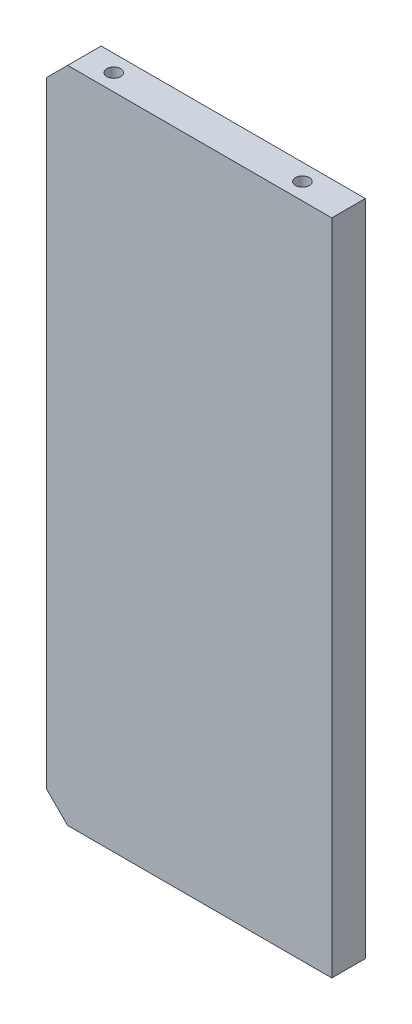
SolidWorks part; units mm, degrees
ref_plane "Front" through (0, 0, 0) normal (0, 0, 1) x (1, 0, 0)
ref_plane "Top" through (0, 0, 0) normal (0, 1, 0) x (1, 0, 0)
ref_plane "Right" through (0, 0, 0) normal (1, 0, 0) x (0, 0, -1)
sketch "Sketch1" plane through (0, 0, 0) normal (0, 0, 1) x (1, 0, 0)
  line L0 (-7.1434, 0) -> (72.4482, 0) construction
  line L2 (68, -78.5) -> (0, -78.5)
  line L3 (68, -78.5) -> (68, 78.5)
  line L4 (68, 78.5) -> (0, 78.5)
  line L5 (0, -78.5) -> (0, 78.5)
  dimension "D1" = 68
  dimension "D2" = 157
extrude "Boss-Extrude1" add sketch "Sketch1" against normal blind 8
hole_wizard "M4x0.7 Tapped Hole1" positions "Sketch5" profile "Sketch4" tap size "M4x0.7" standard "JIS"
sketch "Sketch5" plane through (0, 78.5, 0) normal (0, 1, 0) x (-1, 0, 0)
  point P0 (-12, -4)
  point P2 (-57, -4)
  dimension "D1" = 4
  dimension "D2" = 45
  dimension "D3" = 12
sketch "Sketch4" plane through (12, 78.5, -4) normal (1, 0, 0) x (0, 0, 1)
  line L0 (0, 0) -> (0, 17.0914)
  line L1 (0, 17.0914) -> (1.65, 16.1)
  line L2 (1.65, 16.1) -> (1.65, 0)
  line L5 (1.65, 0) -> (0, 0)
  line L10 (0, 17.0914) -> (-1.65, 16.1) construction
  line L11 (0, -6.35) -> (0, 107.95) construction
  dimension "Tap Drill Dia." = 3.3
  dimension "Tap Drill Depth" = 16.1
  dimension "Drill Angle" = 118
cosmetic thread "Hole Thread4" parameters "D1"=14, "D2"=4
cosmetic thread "Hole Thread5" parameters "D1"=14, "D2"=4
hole_wizard "M4x0.7 Tapped Hole2" positions "Sketch3" profile "Sketch2" tap size "M4x0.7" standard "JIS"
sketch "Sketch3" plane through (0, 0, 0) normal (-1, 0, 0) x (0, 0, 1)
  line L0 (9.2982, 0) -> (-17.8355, 0) construction
  point P0 (-4, 58.5)
  point P1 (-4, 0)
  point P3 (-4, -58.5)
  dimension "D1" = 117
  dimension "D3" = 4
sketch "Sketch2" plane through (0, 58.5, -4) normal (0, 1, 0) x (0, 0, 1)
  line L0 (0, 0) -> (0, 11.0914)
  line L1 (0, 11.0914) -> (1.65, 10.1)
  line L2 (1.65, 10.1) -> (1.65, 0)
  line L5 (1.65, 0) -> (0, 0)
  line L10 (0, 11.0914) -> (-1.65, 10.1) construction
  line L11 (0, -6.35) -> (0, 107.95) construction
  dimension "Tap Drill Dia." = 3.3
  dimension "Tap Drill Depth" = 10.1
  dimension "Drill Angle" = 118
cosmetic thread "Hole Thread1" parameters "D1"=8, "D2"=4
cosmetic thread "Hole Thread2" parameters "D1"=8, "D2"=4
cosmetic thread "Hole Thread3" parameters "D1"=8, "D2"=4
mirror "Mirror1" about plane through (0, 0, 0) normal (0, 1, 0) of "M4x0.7 Tapped Hole1"
chamfer "Chamfer1" distance 5 angle 45 2 edges at (0, -78.5, -4) (0, 78.5, -4)
